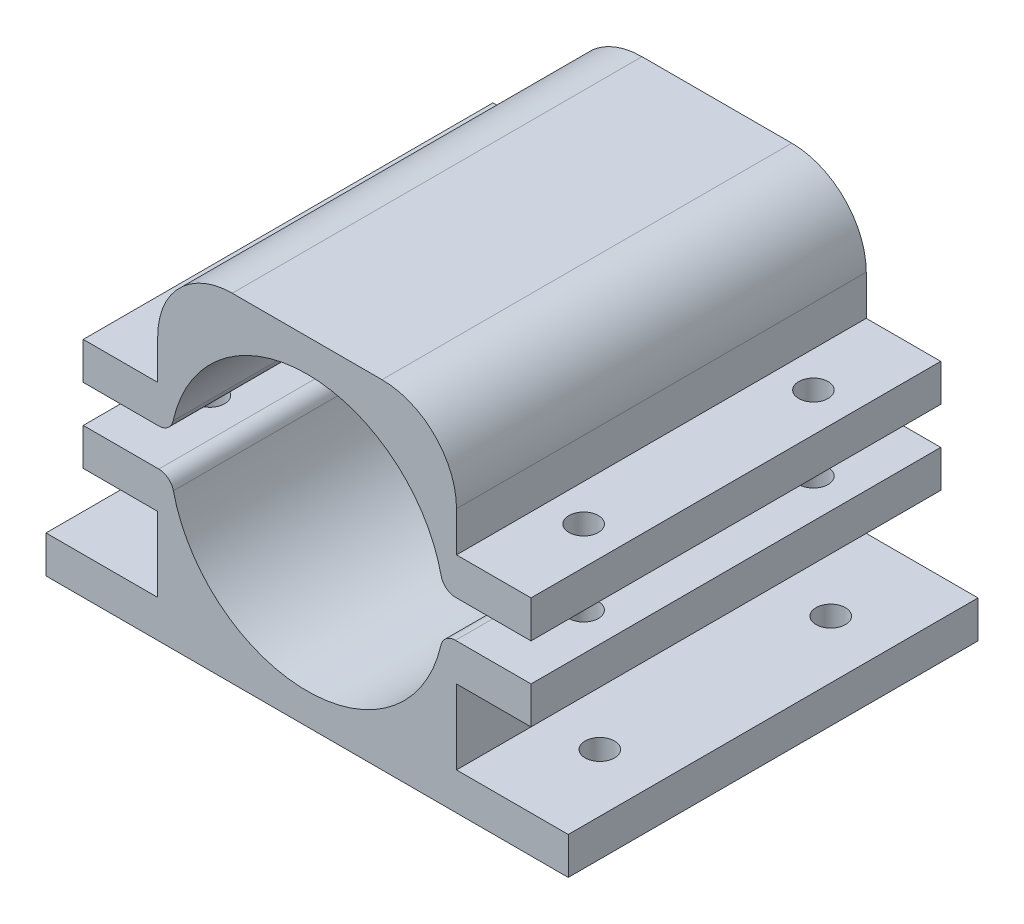
SolidWorks part; units mm, degrees
ref_plane "Front Plane" through (0, 0, 0) normal (0, 0, 1) x (1, 0, 0)
ref_plane "Top Plane" through (0, 0, 0) normal (0, 1, 0) x (1, 0, 0)
ref_plane "Right Plane" through (0, 0, 0) normal (1, 0, 0) x (0, 0, -1)
sketch "Sketch1" plane through (0, 0, 0) normal (0, 0, 1) x (1, 0, 0)
  line L0 (-34.9187, -10.8978) -> (35.1859, -10.8978)
  line L1 (-34.9187, -5.8978) -> (-34.9187, -10.8978)
  line L2 (35.1859, -5.8978) -> (35.1859, -10.8978)
  line L3 (-34.9187, -5.8978) -> (-19.9187, -5.8978)
  line L4 (-19.9187, -5.8978) -> (-19.9187, 4.1022)
  line L5 (-19.9187, 4.1022) -> (-29.9187, 4.1022)
  line L6 (-29.9187, 4.1022) -> (-29.9187, 9.1022)
  line L7 (-29.9187, 9.1022) -> (30.1859, 9.1022)
  line L8 (30.1859, 9.1022) -> (30.1859, 4.1022)
  line L9 (30.1859, 4.1022) -> (20.1859, 4.1022)
  line L10 (20.1859, 4.1022) -> (20.1859, -5.8978)
  line L11 (20.1859, -5.8978) -> (35.1859, -5.8978)
  line L12 (-29.9187, 14.1022) -> (30.1859, 14.1022)
  line L13 (30.1859, 19.1022) -> (30.1859, 14.1022)
  line L14 (30.1859, 19.1022) -> (20.1859, 19.1022)
  line L15 (20.1859, 19.1022) -> (20.1859, 34.4684)
  line L16 (20.1859, 34.4684) -> (-19.9187, 34.4684)
  line L17 (-19.9187, 34.4684) -> (-19.9187, 19.1022)
  line L18 (-19.9187, 19.1022) -> (-29.9187, 19.1022)
  line L19 (-29.9187, 19.1022) -> (-29.9187, 14.1022)
  line L20 (0.1336, -10.8978) -> (0.1336, 11.6723)
  line L21 (20.1859, -5.8978) -> (-19.9187, -5.8978)
  circle A0 centre (0.1336, 11.6723) radius 18.425
  point P21 (30.1859, 16.6022)
  dimension "D14" = 36.85
  dimension "D1" = 5
  dimension "D2" = 5
  dimension "D3" = 15
  dimension "D4" = 15
  dimension "D5" = 10
  dimension "D6" = 10
  dimension "D7" = 5
  dimension "D8" = 10
  dimension "D9" = 10
  dimension "D10" = 10
  dimension "D11" = 10
  dimension "D12" = 0
  dimension "D13" = 0
  dimension "D15" = 5
  dimension "D16" = 5
  dimension "D17" = 5
extrude "Boss-Extrude1" add sketch "Sketch1" along normal blind 55 contours A0 L12 L13 L14 L15 L16 L17 L18 L19 | A0 L20 L0 L2 L11 L21 | A0 L21 L3 L1 L0 L20 | A0 L21 L10 L9 L8 L7 | A0 L7 L6 L5 L4 L21
fillet "Fillet1" radius 10 2 edges at (20.1859, 34.4684, 27.5) (-19.9187, 34.4684, 27.5)
fillet "Fillet2" radius 2 2 edges at (-18.1113, 9.1022, 27.5) (18.3785, 9.1022, 27.5)
fillet "Fillet3" radius 2 2 edges at (-18.1305, 14.1022, 27.5) (18.3977, 14.1022, 27.5)
sketch "Sketch3" plane through (0, 19.1022, 0) normal (0, 1, 0) x (1, 0, 0)
  line L0 (-19.9187, -55) -> (-29.9187, -55) construction
  line L2 (-19.9187, 0) -> (-29.9187, 0) construction
  line L3 (0, 0) -> (0.1336, -55) construction
  line L4 (10.1859, -55) -> (-9.9187, -55) construction
  circle A0 centre (-24.9187, -12) radius 1.975
  circle A1 centre (-24.9187, -43) radius 1.975
  circle A3 centre (25.1273, -42.8784) radius 1.975
  circle A4 centre (24.9767, -11.8788) radius 1.975
  dimension "D1" = 3.95
  dimension "D2" = 3.95
  dimension "D3" = 12
  dimension "D4" = 12
extrude "Cut-Extrude1" cut sketch "Sketch3" against normal up to surface (15 mm away) up to face at (-24.9187, 4.1022, 27.5)
sketch "Sketch5" plane through (0, -10.8978, 0) normal (0, -1, 0) x (-1, 0, 0)
  line L0 (34.9187, 0) -> (19.9187, 0) construction
  line L1 (34.9187, 0) -> (-35.1859, 0) construction
  line L2 (27.4187, 0) -> (27.4187, -55) construction
  line L3 (34.9187, -55) -> (-35.1859, -55) construction
  line L4 (0, -55) -> (0, 0) construction
  circle A0 centre (27.4187, -43) radius 1.975
  circle A1 centre (27.4187, -12) radius 1.975
  circle A2 centre (-27.4187, -12) radius 1.975
  circle A3 centre (-27.4187, -43) radius 1.975
  dimension "D2" = 3.95
  dimension "D3" = 3.95
  dimension "D4" = 12
  dimension "D5" = 12
  dimension "D1" = 15
extrude "Cut-Extrude2" cut sketch "Sketch5" against normal up to surface (5 mm away) up to face at (27.6859, -5.8978, 27.5)
